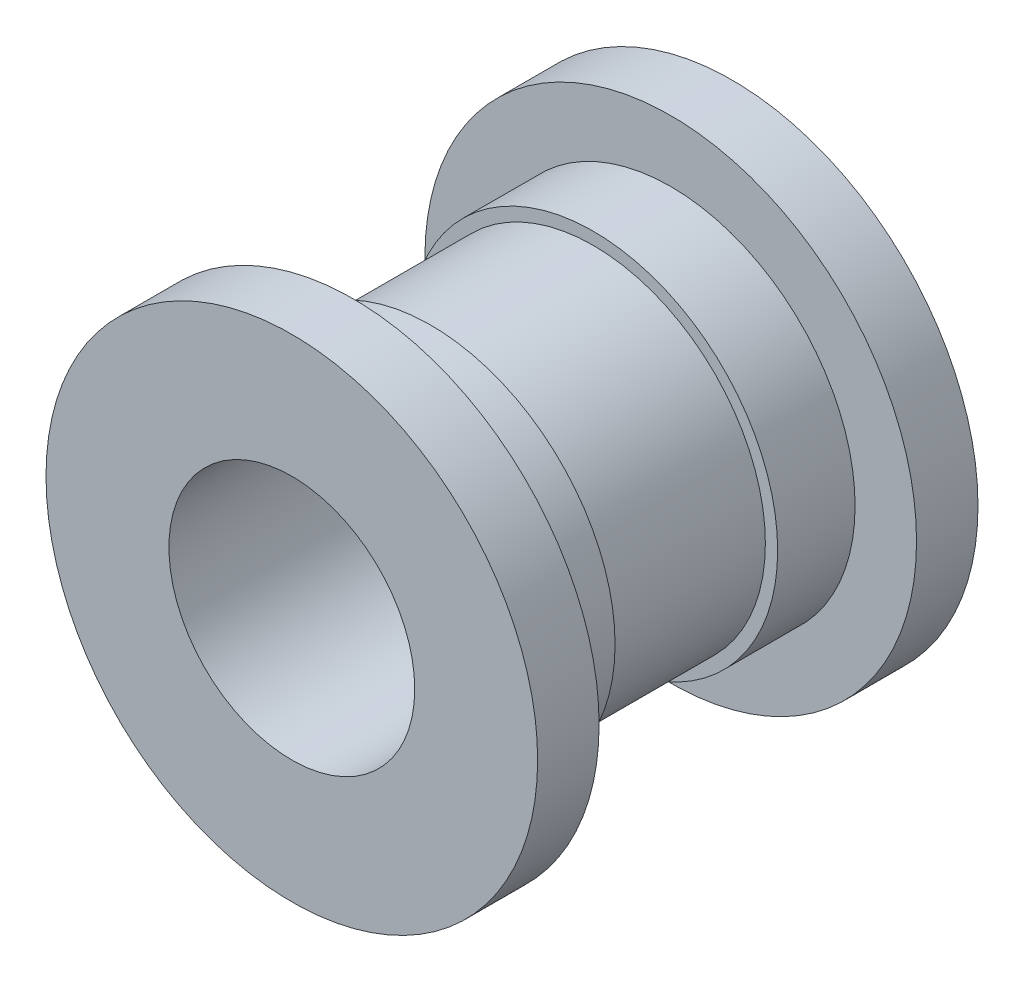
SolidWorks part; units mm, degrees
ref_plane "Front Plane" through (0, 0, 0) normal (0, 0, 1) x (1, 0, 0)
ref_plane "Top Plane" through (0, 0, 0) normal (0, 1, 0) x (1, 0, 0)
ref_plane "Right Plane" through (0, 0, 0) normal (1, 0, 0) x (0, 0, -1)
sketch "Sketch1" plane through (0, 0, 0) normal (0, 0, 1) x (1, 0, 0)
  circle A0 centre (0, 0) radius 4.445
  dimension "D1" = 8.89
extrude "Boss-Extrude1" add sketch "Sketch1" along normal blind 2.1
sketch "Sketch2" plane through (0, 0, 2.1) normal (0, 0, 1) x (1, 0, 0)
  circle A1 centre (0, 0) radius 4.7625
  dimension "D1" = 9.525
extrude "Boss-Extrude2" add sketch "Sketch2" along normal blind 2
sketch "Sketch4" plane through (0, 0, 4.1) normal (0, 0, 1) x (1, 0, 0)
  circle A0 centre (0, 0) radius 6.35
  dimension "D1" = 12.7
extrude "Boss-Extrude4" add sketch "Sketch4" along normal blind 1.5875
mirror "Mirror1" about plane through (0, 0, 0) normal (0, 0, 1) of "Boss-Extrude4", "Boss-Extrude1", "Boss-Extrude2"
sketch "Sketch5" plane through (0, 0, 5.6875) normal (0, 0, 1) x (1, 0, 0)
  circle A0 centre (0, 0) radius 3.175
  dimension "D1" = 6.35
extrude "Cut-Extrude1" cut sketch "Sketch5" against normal through all
